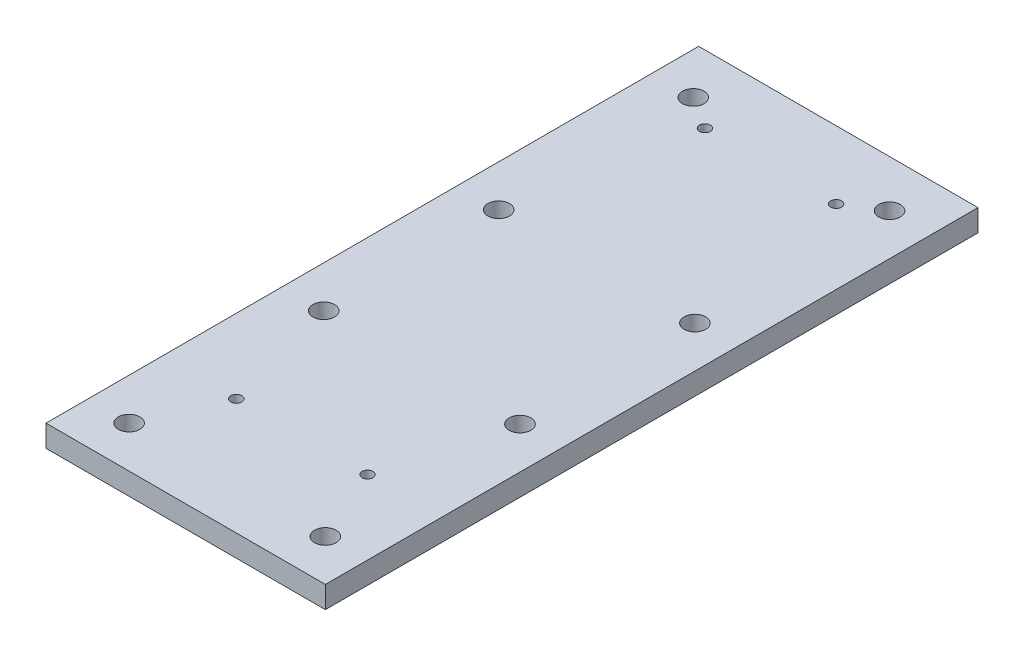
SolidWorks part; units mm, degrees
ref_plane "Front Plane" through (0, 0, 0) normal (0, 0, 1) x (1, 0, 0)
ref_plane "Top Plane" through (0, 0, 0) normal (0, 1, 0) x (1, 0, 0)
ref_plane "Right Plane" through (0, 0, 0) normal (1, 0, 0) x (0, 0, -1)
sketch "Sketch1" plane through (0, 0, 0) normal (0, 1, 0) x (1, 0, 0)
  line L1 (0, 0) -> (127.75, 0)
  line L2 (0, 0) -> (0, 298.45)
  line L3 (0, 298.45) -> (127.75, 298.45)
  line L4 (127.75, 0) -> (127.75, 298.45)
  line L5 (0, 0) -> (127.75, 298.45) construction
  line L6 (0, 298.45) -> (127.75, 0) construction
  circle A0 centre (19, 277) radius 4.95
  circle A1 centre (108.75, 277) radius 4.95
  circle A4 centre (108.75, 19) radius 4.95
  circle A7 centre (19, 19) radius 4.95
  circle A8 centre (19, 105) radius 4.95 [skipped]
  circle A9 centre (108.75, 105) radius 4.95 [skipped]
  circle A10 centre (19, 108) radius 4.95
  circle A11 centre (108.75, 108) radius 4.95
  circle A12 centre (108.75, 191) radius 4.95 [skipped]
  circle A13 centre (19, 191) radius 4.95 [skipped]
  circle A14 centre (19, 188) radius 4.95
  circle A16 centre (108.75, 188) radius 4.95
  point P4 (63.875, 149.225)
  point P10 (0, 0)
  point P15 (0, 0)
  point P16 (0, 0)
  dimension "D5" = 9.9
  dimension "D1" = 127.75
  dimension "D2" = 298.45
  dimension "D6" = 89
  dimension "D7" = 19
  dimension "D8" = 19
  dimension "D9" = 19
  dimension "D10" = 80
  dimension "D11" = 89
  dimension "D3" = 2
  dimension "D4" = 4
extrude "Boss-Extrude1" add sketch "Sketch1" along normal blind 10
sketch "Sketch4" plane through (0, 10, 0) normal (0, 1, 0) x (1, 0, 0)
  line L0 (63.875, 298.45) -> (63.875, 267.45) construction
  line L2 (127.75, 298.45) -> (0, 298.45) construction
  line L3 (93.875, 267.45) -> (33.875, 267.45) construction
  line L4 (93.875, 267.45) -> (93.875, 53.1375) construction
  line L5 (93.875, 53.1375) -> (33.875, 53.1375) construction
  line L6 (33.875, 53.1375) -> (33.875, 267.45) construction
  circle A0 centre (93.875, 267.45) radius 2.5
  circle A1 centre (33.875, 267.45) radius 2.5
  circle A2 centre (93.875, 53.1375) radius 2.5
  circle A3 centre (33.875, 53.1375) radius 2.5
  point P7 (63.875, 267.45)
  point P10 (63.875, 298.45)
  dimension "D4" = 5
  dimension "D1" = 60
  dimension "D2" = 31
  dimension "D3" = 214.3125
extrude "Cut-Extrude2" cut sketch "Sketch4" against normal through all
sketch "Sketch2" plane through (0, 10, 0) normal (0, 1, 0) x (1, 0, 0)
  line L0 (33.875, 31) -> (93.875, 31) construction
  line L1 (33.875, 31) -> (33.875, 245.3125) construction
  line L2 (63.875, 0) -> (63.875, 31) construction
  line L3 (0, 0) -> (127.75, 0) construction
  line L6 (19, 19) -> (19, 0) construction
  line L7 (93.875, 31) -> (93.875, 245.3125) construction
  line L8 (93.875, 245.3125) -> (33.875, 245.3125) construction
  line L9 (127.75, 0) -> (127.75, 31) construction
  line L10 (127.75, 0) -> (127.75, 298.45) construction
  line L11 (127.75, 31) -> (93.875, 31) construction
  circle A0 centre (33.875, 31) radius 2.5
  circle A1 centre (93.875, 31) radius 2.5
  circle A2 centre (33.875, 245.3125) radius 2.5
  circle A3 centre (93.875, 245.3125) radius 2.5
  point P7 (63.875, 31)
  point P21 (0, 0)
  dimension "D3" = 5
  dimension "D1" = 31
  dimension "D2" = 60
  dimension "D4" = 214.3125
extrude "Cut-Extrude1" [suppressed] cut sketch "Sketch2" against normal through all
sketch "Sketch3" plane through (0, 10, 0) normal (0, 1, 0) x (1, 0, 0)
  line L0 (0, 0) -> (230.4164, 0) construction
  line L1 (127.75, 298.45) -> (127.75, -59.1882) construction
  line L2 (129.3375, -1.5875) -> (-5.1025, -1.5875) construction
  line L3 (129.3375, -1.5875) -> (129.3375, 341.7487) construction
  circle A0 centre (129.3375, -1.5875) radius 1.5875
  dimension "D1" = 3.175
sketch "Sketch5" plane through (0, 10, 0) normal (0, 1, 0) x (1, 0, 0)
  line L0 (33.875, 267.45) -> (0, 298.45) construction
  line L1 (0, 298.45) -> (0, 267.45) construction
  line L2 (0, 298.45) -> (0, 0) construction
  line L3 (0, 267.45) -> (33.875, 267.45) construction
sketch "Sketch6" plane through (0, 10, 0) normal (0, 1, 0) x (1, 0, 0)
  line L0 (33.875, 267.45) -> (33.875, 229.45) construction
  line L1 (111.375, 229.45) -> (16.375, 229.45) construction
  line L2 (16.375, 229.45) -> (16.375, 194.45) construction
  line L3 (16.375, 229.45) -> (0, 229.45) construction
  line L4 (0, 298.45) -> (0, 0) construction
  line L5 (127.75, 229.45) -> (111.375, 229.45) construction
  line L6 (127.75, 0) -> (127.75, 298.45) construction
  line L7 (33.875, 267.45) -> (16.375, 267.45) construction
  line L8 (16.375, 267.45) -> (16.375, 229.45) construction
  dimension "D1" = 38
  dimension "D2" = 35
  dimension "D3" = 95
